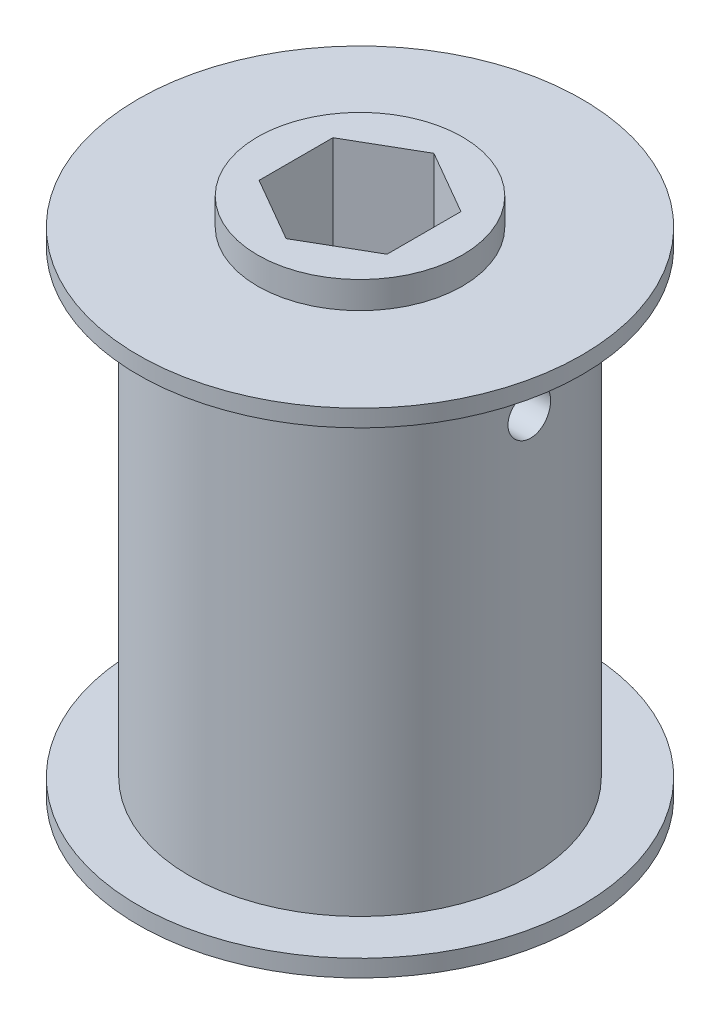
SolidWorks part; units mm, degrees
material "6061 Alloy"
ref_plane "Front Plane" through (0, 0, 0) normal (0, 0, 1) x (1, 0, 0)
ref_plane "Top Plane" through (0, 0, 0) normal (0, 1, 0) x (1, 0, 0)
ref_plane "Right Plane" through (0, 0, 0) normal (1, 0, 0) x (0, 0, -1)
sketch "Sketch1" plane through (0, 0, 0) normal (0, 0, 1) x (1, 0, 0)
  line L1 (-7.62, 18.3642) -> (-16.51, 18.3642)
  line L2 (-16.51, 18.3642) -> (-16.51, 17.0942)
  line L3 (-16.51, 17.0942) -> (-12.7, 17.0942)
  line L4 (-12.7, 17.0942) -> (-12.7, -17.0942)
  line L5 (-12.7, -17.0942) -> (-16.51, -17.0942)
  line L6 (-16.51, -17.0942) -> (-16.51, -18.3642)
  line L7 (-16.51, -18.3642) -> (-7.62, -18.3642)
  line L9 (0, -20.3708) -> (-7.62, -20.3708)
  line L10 (-7.62, -20.3708) -> (-7.62, -18.3642)
  line L12 (0, 20.3708) -> (-7.62, 20.3708)
  line L13 (-7.62, 20.3708) -> (-7.62, 18.3642)
  line L14 (0, 20.3708) -> (0, -20.3708)
  point P1 (0, 0)
  dimension "D1" = 40.7416
  dimension "D3" = 1.27
  dimension "D4" = 3.81
  dimension "D5" = 12.7
  dimension "D6" = 7.62
  dimension "D7" = 2.0066
revolve "Revolve1" add sketch "Sketch1" angle 360 about L14
sketch "Sketch2" plane through (0, 20.3708, 0) normal (0, 1, 0) x (1, 0, 0)
  line L1 (0, 5.4993) -> (-4.7625, 2.7496)
  line L2 (-4.7625, 2.7496) -> (-4.7625, -2.7496)
  line L3 (-4.7625, -2.7496) -> (0, -5.4993)
  line L4 (0, -5.4993) -> (4.7625, -2.7496)
  line L5 (4.7625, -2.7496) -> (4.7625, 2.7496)
  line L6 (4.7625, 2.7496) -> (0, 5.4993)
  circle A0 centre (0, 0) radius 4.7625 construction
  dimension "D1" = 9.525
extrude "Cut-Extrude1" cut sketch "Sketch2" against normal through all
sketch "Sketch3" plane through (0, 0, 0) normal (1, 0, 0) x (0, 0, -1)
  circle A0 centre (0, 12.7) radius 1.5875
  dimension "D1" = 3.175
  dimension "D2" = 12.7
extrude "Cut-Extrude2" cut sketch "Sketch3" against normal through all both and the other way through all
